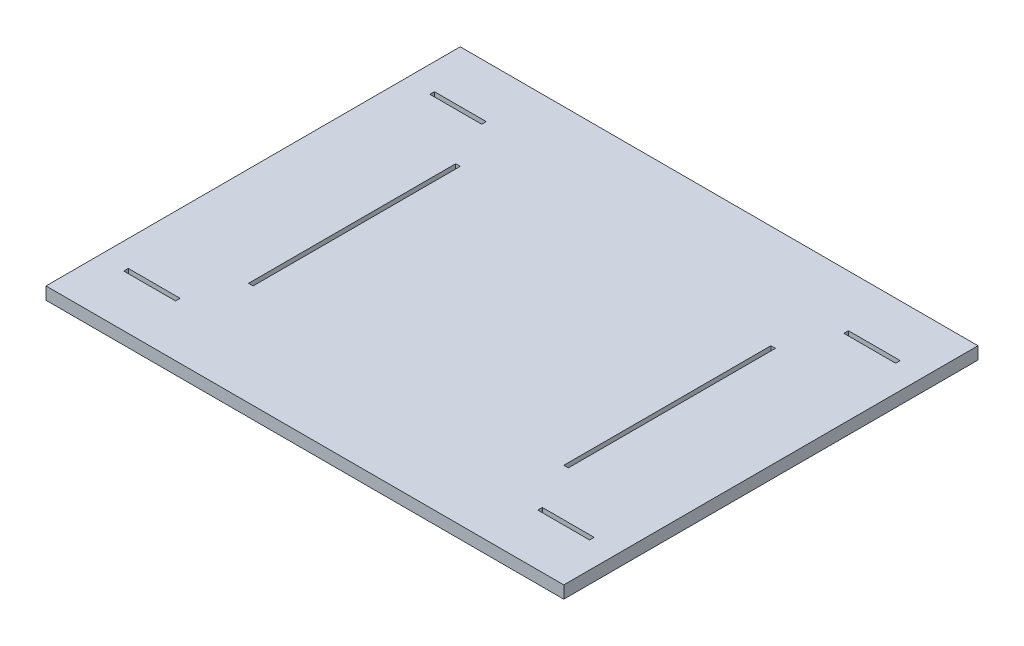
SolidWorks part; units mm, degrees
ref_plane "Front Plane" through (0, 0, 0) normal (0, 0, 1) x (1, 0, 0)
ref_plane "Top Plane" through (0, 0, 0) normal (0, 1, 0) x (1, 0, 0)
ref_plane "Right Plane" through (0, 0, 0) normal (1, 0, 0) x (0, 0, -1)
sketch "Sketch1" plane through (0, 0, 0) normal (0, 1, 0) x (1, 0, 0)
  line L1 (-250, 200) -> (250, 200)
  line L2 (-250, 200) -> (-250, -200)
  line L3 (-250, -200) -> (250, -200)
  line L4 (250, 200) -> (250, -200)
  line L5 (-250, 200) -> (250, -200) construction
  line L6 (-250, -200) -> (250, 200) construction
  point P0 (0, 0)
  dimension "D1" = 500
  dimension "D2" = 400
extrude "Boss-Extrude1" add sketch "Sketch1" along normal blind 12 contours L2 L3 L4 L1
sketch "Sketch2" plane through (0, 12, 0) normal (0, 1, 0) x (1, 0, 0)
  line L0 (-6.6, 0) -> (6.6, 0) construction
  line L1 (-154.4, 100) -> (-150, 100)
  line L2 (-154.4, 100) -> (-154.4, -100)
  line L3 (-154.4, -100) -> (-150, -100)
  line L4 (-150, 100) -> (-150, -100)
  line L5 (-154.4, 100) -> (-150, -100) construction
  line L6 (-154.4, -100) -> (-150, 100) construction
  line L8 (0, -6.6) -> (0, 6.6) construction
  point P0 (-152.2, 0)
  dimension "D1" = 200
  dimension "D2" = 4.4
  dimension "D3" = 150
extrude "Cut-Extrude1" cut sketch "Sketch2" against normal up to surface (12 mm away) contours L4 L3 L2 L1 up to face at (0, 0, 0)
mirror "Mirror2" about plane through (0, 0, 0) normal (1, 0, 0) of "Cut-Extrude1"
sketch "Sketch5" plane through (0, 12, 0) normal (0, 1, 0) x (1, 0, 0)
  line L0 (-154.4, 100) -> (-154.4, -100) construction
  line L1 (-224.9, 150) -> (-174.9, 150)
  line L2 (-224.9, 150) -> (-224.9, 145.6)
  line L3 (-224.9, 145.6) -> (-174.9, 145.6)
  line L4 (-174.9, 150) -> (-174.9, 145.6)
  line L5 (-224.9, 150) -> (-174.9, 145.6) construction
  line L6 (-224.9, 145.6) -> (-174.9, 150) construction
  line L7 (-250, 200) -> (250, 200) construction
  point P0 (-199.9, 147.8)
  dimension "D1" = 4.4
  dimension "D2" = 50
  dimension "D3" = 20.5
  dimension "D4" = 50
extrude "Cut-Extrude2" cut sketch "Sketch5" against normal up to surface (12 mm away) up to face at (152.2, 0, 0)
mirror "Mirror5" about plane through (0, 0, 0) normal (0, 0, 1) of "Cut-Extrude2" second plane through (0, 0, 0) second plane normal (1, 0, 0)
